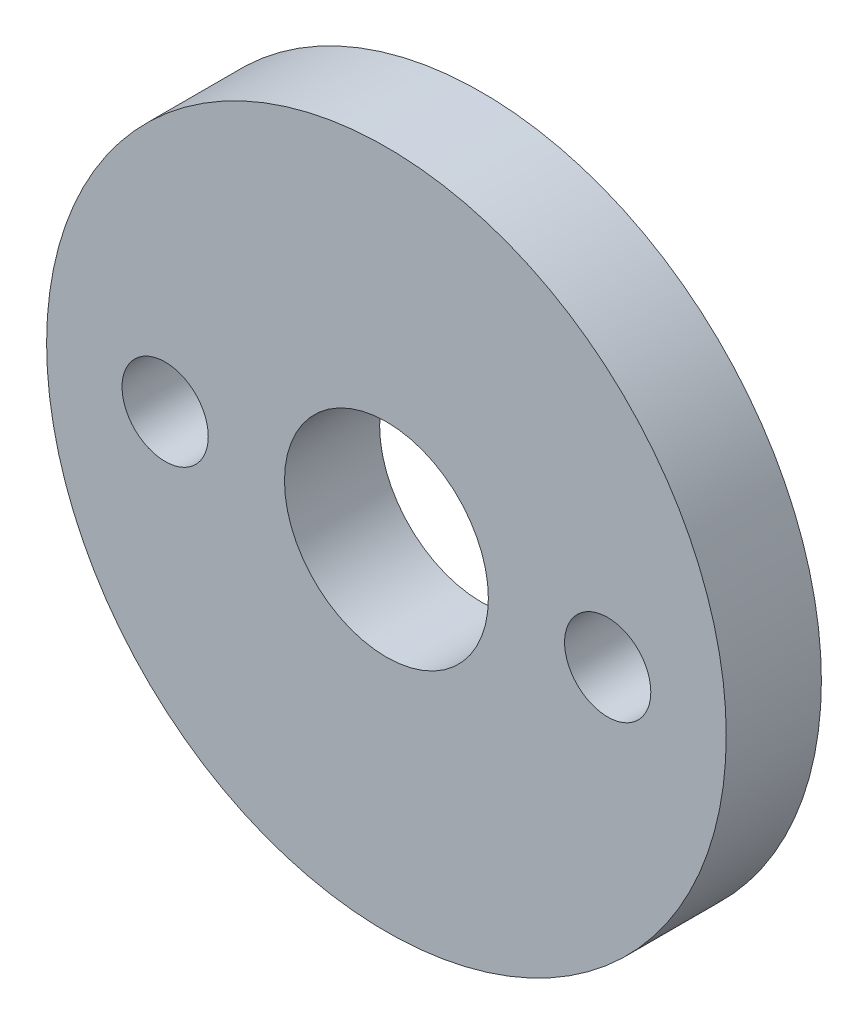
SolidWorks part; units mm, degrees
ref_plane "Front Plane" through (0, 0, 0) normal (0, 0, 1) x (1, 0, 0)
ref_plane "Top Plane" through (0, 0, 0) normal (0, 1, 0) x (1, 0, 0)
ref_plane "Right Plane" through (0, 0, 0) normal (1, 0, 0) x (0, 0, -1)
sketch "Sketch1" plane through (0, 0, 0) normal (0, 0, 1) x (1, 0, 0)
  circle A0 centre (0, 0) radius 11.43
  circle A1 centre (0, 0) radius 3.429
  dimension "D1" = 22.86
  dimension "D2" = 6.858
extrude "Boss-Extrude1" add sketch "Sketch1" along normal blind 3.2004
sketch "Sketch2" plane through (0, 0, 3.2004) normal (0, 0, 1) x (1, 0, 0)
  line L2 (-7.4422, 0) -> (7.4422, 0) construction
  circle A2 centre (-7.4422, 0) radius 1.45
  circle A3 centre (7.4422, 0) radius 1.45
  circle A6 centre (0, 0) radius 11.43 construction
  point P17 (0, 0)
  dimension "D4" = 2.9
  dimension "D5" = 14.8844
extrude "Cut-Extrude1" cut sketch "Sketch2" against normal up to surface (3.2004 mm away) up to face at (11.43, 0, 0)
